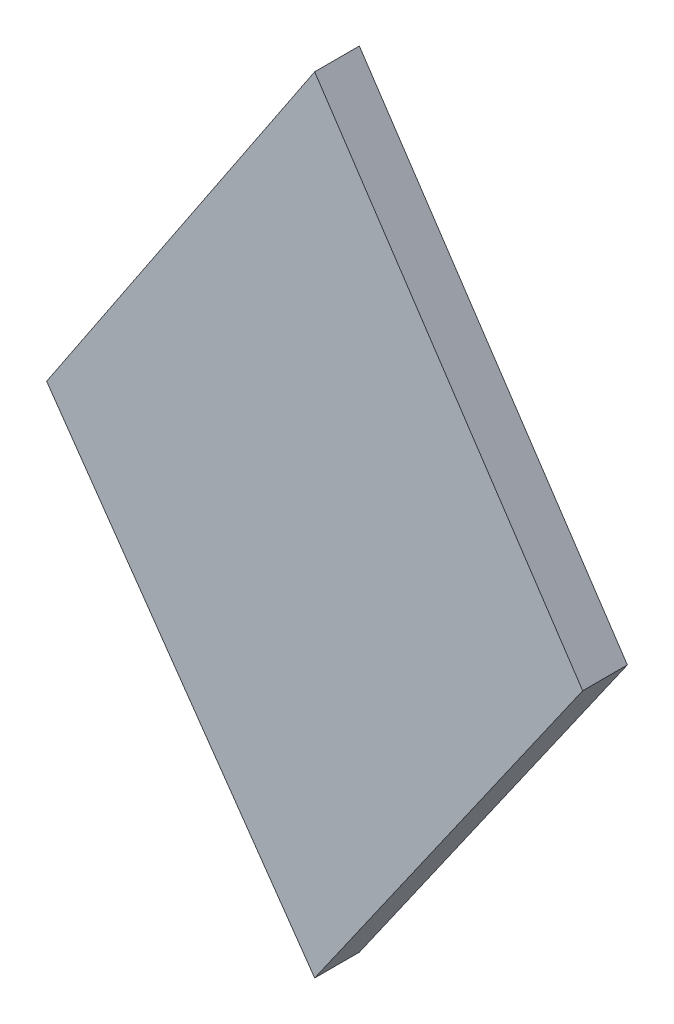
SolidWorks part; units mm, degrees
ref_plane "Front" through (0, 0, 0) normal (0, 0, 1) x (1, 0, 0)
ref_plane "Top" through (0, 0, 0) normal (0, 1, 0) x (1, 0, 0)
ref_plane "Right" through (0, 0, 0) normal (1, 0, 0) x (0, 0, -1)
sketch "Sketch1" plane through (0, 0, 0) normal (0, 0, 1) x (1, 0, 0)
  line L0 (0, 45) -> (30, 0)
  line L1 (30, 0) -> (0, -42.8444)
  line L2 (0, -42.8444) -> (-30, 0)
  line L3 (-30, 0) -> (0, 45)
  line L5 (0, -50) -> (0, 50) construction
  line L6 (50, 0) -> (-50, 0) construction
  dimension "D1" = 45
  dimension "D2" = 55
  dimension "D3" = 60
  dimension "D4" = 30
extrude "Boss-Extrude1" add sketch "Sketch1" along normal blind 5
